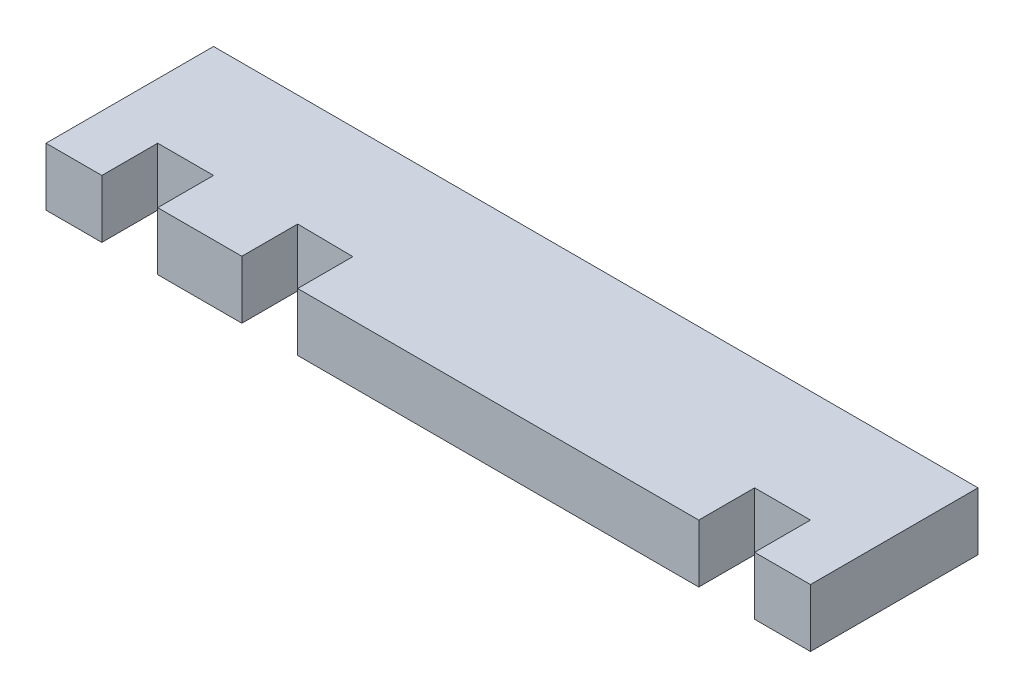
SolidWorks part; units mm, degrees
ref_plane "Front Plane" through (0, 0, 0) normal (0, 0, 1) x (1, 0, 0)
ref_plane "Top Plane" through (0, 0, 0) normal (0, 1, 0) x (1, 0, 0)
ref_plane "Right Plane" through (0, 0, 0) normal (1, 0, 0) x (0, 0, -1)
sketch "Sketch1" plane through (0, 0, 0) normal (0, 1, 0) x (1, 0, 0)
  line L0 (-26.35, 0) -> (26.35, 0) construction
  line L1 (-26.35, -5.775) -> (26.35, -5.775) construction
  line L2 (-26.35, -5.775) -> (-26.35, 5.775) construction
  line L3 (-26.35, 5.775) -> (26.35, 5.775)
  line L4 (26.35, -5.775) -> (26.35, 5.775) construction
  line L5 (-26.35, -5.775) -> (26.35, 5.775) construction
  line L6 (-26.35, 5.775) -> (26.35, -5.775) construction
  line L7 (-26.35, 5.775) -> (-26.35, -5.775)
  line L8 (-26.35, -5.775) -> (-22.5, -5.775)
  line L9 (-22.5, -5.775) -> (-22.5, -1.925)
  line L10 (-22.5, -1.925) -> (-18.65, -1.925)
  line L11 (-18.65, -1.925) -> (-18.65, -5.775)
  line L17 (-12.8497, -5.775) -> (-12.8497, -1.925)
  line L18 (-12.8497, -1.925) -> (-9, -1.9725)
  line L19 (-9, -1.9725) -> (-9, -5.775)
  line L25 (18.65, -5.775) -> (18.65, -1.925)
  line L26 (18.65, -1.925) -> (22.5, -1.925)
  line L27 (22.5, -1.925) -> (22.5, -5.775)
  line L28 (22.5, -5.775) -> (26.35, -5.775)
  line L29 (26.35, -5.775) -> (26.35, 5.775)
  line L30 (-18.65, -5.775) -> (-12.8497, -5.775)
  line L31 (18.65, -5.775) -> (-9, -5.775)
  line L32 (-26.35, -1.925) -> (26.35, -1.925) construction
  point P0 (0, 0)
  dimension "D1" = 11.55
  dimension "D3" = 3.85
  dimension "D2" = 13.5
  dimension "D4" = 31.5
  dimension "D5" = 3.85
extrude "Boss-Extrude1" add sketch "Sketch1" along normal blind 4
equation "\"m3_hole\"= 3.5"
equation "\"m3_washer\"= 7.3"
equation "\"m3_nut\"= 5.3"
equation "\"plywood_thickness\" = 3.85"
equation "\"guide_width\"= 10.0"
equation "\"guide_length\"= 65.0"
equation "\"guide_tab_length\" = 10.0"
equation "\"guide_tab_width\" = 9.0"
equation "\"guide_thickness\" = 12.0"
equation "\"grinder_od\"= 52.0"
equation "\"grinder_id\"= 45.5"
equation "\"grinder_adjust_od\" = 58.0"
equation "\"funnel_width_from_adjust_ring\" = 13.0"
equation "\"drill_contact_diameter_small\" = 24.0"
equation "\"drill_contact_diameter_medium\" = 28.0"
equation "\"drill_contact_diameter_large\" = 39.0"
equation "\"drill_contact_diameter_tab\" = 31.0"
equation "\"drill_contact_ow_tab\" = 14.5"
equation "\"drill_contact_iw_tab\" = 8.7"
equation "\"drill_contact_small_height\" = 15.5"
equation "\"drill_contact_large_height\" = 34.5"
equation "\"plywood_peg_length\" = 40"
equation "\"plywood_peg_width\" = 8.3"
equation "\"D1@Sketch1\"=\"plywood_thickness\"*3"
equation "\"D3@Sketch1\"=\"plywood_thickness\""
equation "\"D5@Sketch1\"=\"plywood_thickness\""
